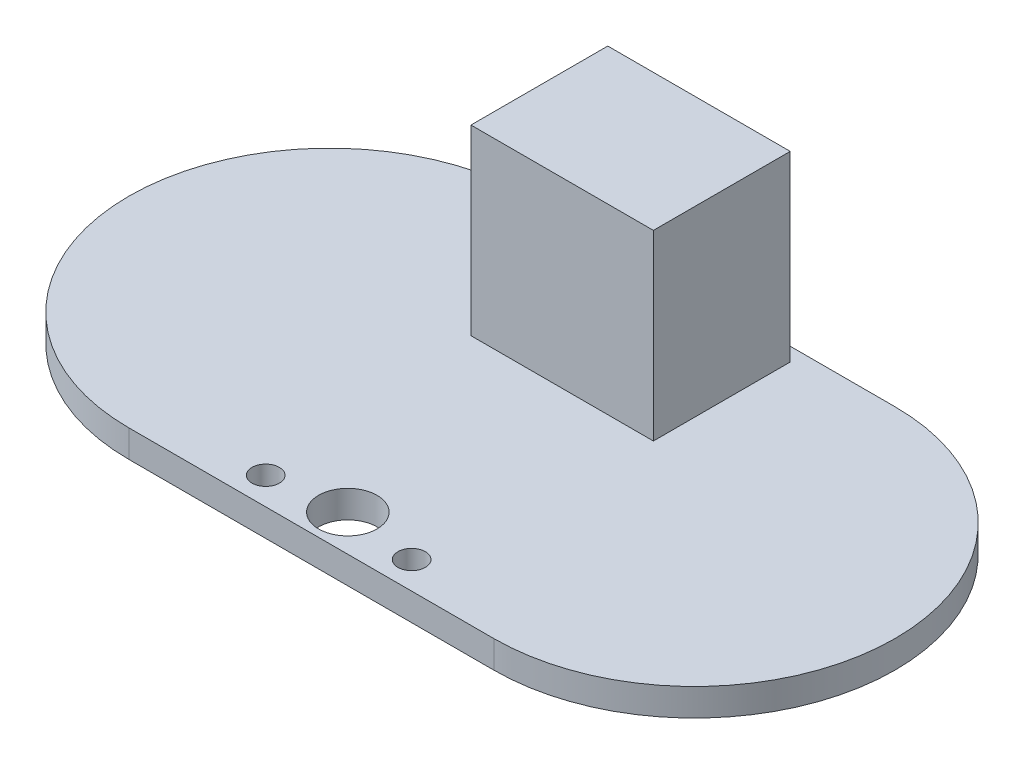
SolidWorks part; units mm, degrees
ref_plane "Front Plane" through (0, 0, 0) normal (0, 0, 1) x (1, 0, 0)
ref_plane "Top Plane" through (0, 0, 0) normal (0, 1, 0) x (1, 0, 0)
ref_plane "Right Plane" through (0, 0, 0) normal (1, 0, 0) x (0, 0, -1)
sketch "Sketch1" plane through (0, 0, 0) normal (0, 1, 0) x (1, 0, 0)
  line L0 (-10, 0) -> (10, 0)
  line L1 (10, 0) -> (21, 0)
  line L2 (10, 11) -> (-10, 11)
  line L3 (0, 11) -> (0, -11)
  line L4 (27.4505, 0) -> (-35.0474, 0) construction
  line L5 (0, 19.4737) -> (0, -23.8042) construction
  line L6 (-10, 0) -> (-21, 0)
  line L7 (10, -11) -> (-10, -11)
  arc A0 (10, -11) -> (10, 11) centre (10, 0) ccw
  arc A1 (-10, -11) -> (-10, 11) centre (-10, 0) cw
  point P16 (0, 0)
  dimension "D1" = 11
  dimension "D2" = 10
extrude "Boss-Extrude1" add sketch "Sketch1" along normal blind 1.5 contours A1 L6 L0 L3 L2 | A1 L7 L3 L0 L6 | L7 A0 L1 L0 L3 | L1 A0 L2 L3 L0
sketch "Sketch2" plane through (0, 1.5, 0) normal (0, 1, 0) x (1, 0, 0)
  line L0 (10, 11) -> (-10, 11) construction
  line L1 (-5, 10.25) -> (5, 10.25)
  line L2 (-5, 10.25) -> (-5, 2.75)
  line L3 (-5, 2.75) -> (5, 2.75)
  line L4 (5, 10.25) -> (5, 2.75)
  line L5 (-5, 10.25) -> (5, 2.75) construction
  line L6 (-5, 2.75) -> (5, 10.25) construction
  point P0 (0, 6.5)
  dimension "D1" = 0.75
  dimension "D2" = 10
  dimension "D3" = 7.5
extrude "Boss-Extrude2" add sketch "Sketch2" along normal blind 10
sketch "Sketch3" plane through (0, 1.5, 0) normal (0, 1, 0) x (1, 0, 0)
  line L0 (10, -11) -> (-10, -11) construction
  circle A0 centre (0, -9) radius 1.6
  circle A1 centre (-4, -9.5) radius 0.75
  circle A2 centre (4, -9.5) radius 0.75
  dimension "D2" = 3.2
  dimension "D5" = 1.5
  dimension "D6" = 1.5
  dimension "D1" = 2
  dimension "D3" = 1.5
  dimension "D4" = 1.5
  dimension "D7" = 4
  dimension "D8" = 4
extrude "Cut-Extrude1" cut sketch "Sketch3" against normal through all
